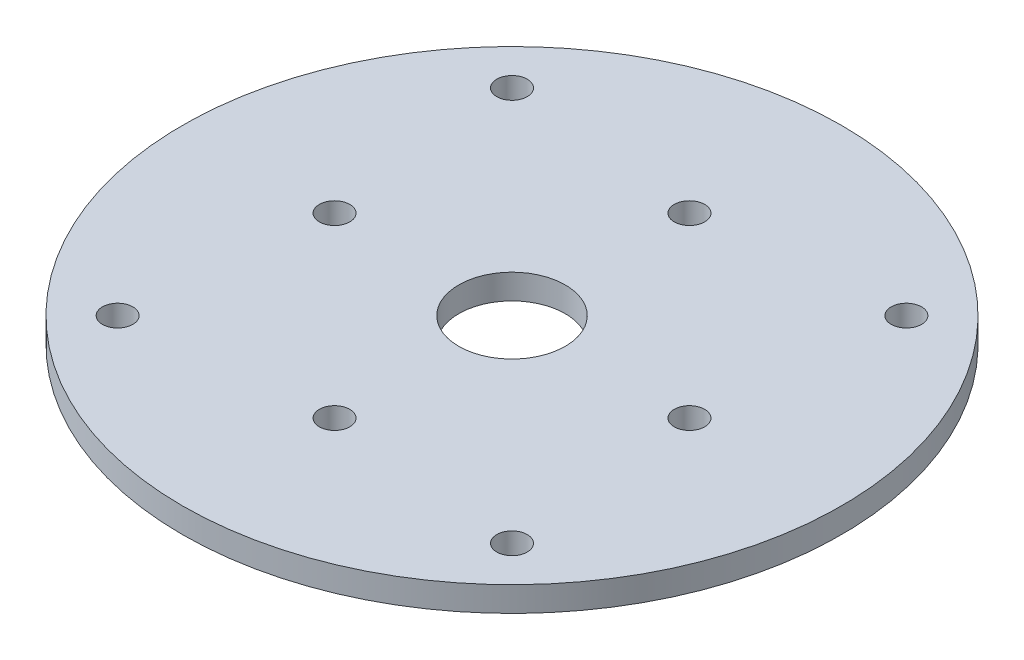
SolidWorks part; units mm, degrees
ref_plane "前基準面" through (0, 0, 0) normal (0, 0, 1) x (1, 0, 0)
ref_plane "上基準面" through (0, 0, 0) normal (0, 1, 0) x (1, 0, 0)
ref_plane "右基準面" through (0, 0, 0) normal (1, 0, 0) x (0, 0, -1)
sketch "草圖1" plane through (0, 0, 0) normal (0, 1, 0) x (1, 0, 0)
  line L0 (0, 0) -> (0, 75.702) construction
  line L1 (0, 75.702) -> (0, -85.4399) construction
  line L2 (0, 0) -> (137.2261, 0) construction
  line L3 (137.2261, 0) -> (-111.8072, 0) construction
  circle A0 centre (0, 0) radius 10.5
  circle A1 centre (0, 0) radius 65
  circle A2 centre (0, 35) radius 3
  circle A3 centre (0, -35) radius 3
  circle A4 centre (35, 0) radius 3
  circle A5 centre (-35, 0) radius 3
  dimension "D1" = 21
  dimension "D2" = 130
  dimension "D7" = 6
  dimension "D8" = 6
  dimension "D9" = 6
  dimension "D10" = 6
  dimension "D3" = 35
  dimension "D4" = 35
  dimension "D5" = 35
  dimension "D6" = 35
extrude "填料-伸長3" add sketch "草圖1" along normal blind 4.917 contours A1 A5 A4 A3 A2 A0
sketch "Sketch1" plane through (0, 4.917, 0) normal (0, 1, 0) x (1, 0, 0)
  line L0 (0, 0) -> (0, 99.4266) construction
  line L1 (0, 0) -> (-78.2687, 78.2687) construction
  circle A0 centre (0, 0) radius 55 construction
  circle A1 centre (-38.8909, 38.8909) radius 3
  dimension "D1" = 110
  dimension "D2" = 6
  dimension "D3" = 45
extrude "Cut-Extrude1" cut sketch "Sketch1" against normal through all and the other way through all
pattern_circular "CirPattern1" count 4 over 360 about axis through (0, 0, 0) along (0, 1, 0) of "Cut-Extrude1"
